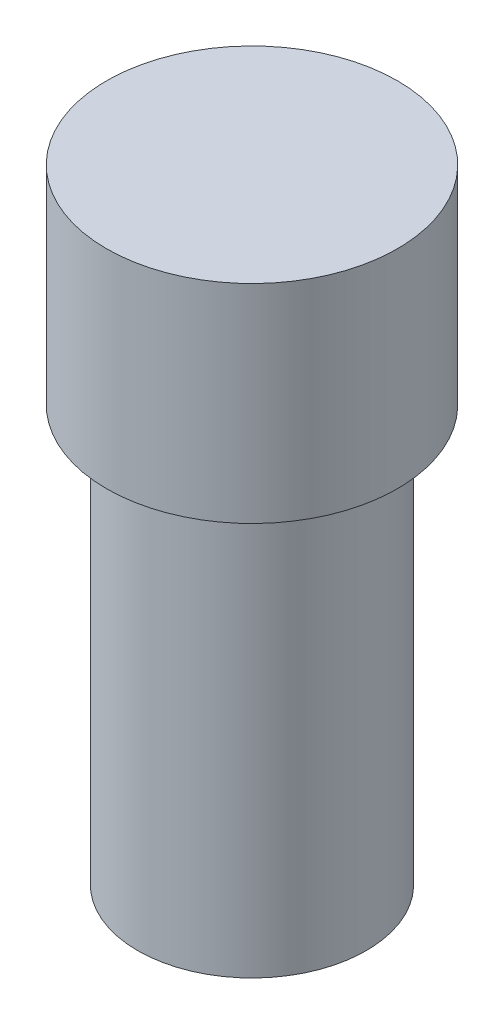
SolidWorks part; units mm, degrees
ref_plane "Front Plane" through (0, 0, 0) normal (0, 0, 1) x (1, 0, 0)
ref_plane "Top Plane" through (0, 0, 0) normal (0, 1, 0) x (1, 0, 0)
ref_plane "Right Plane" through (0, 0, 0) normal (1, 0, 0) x (0, 0, -1)
sketch "Sketch1" plane through (0, 0, 0) normal (0, 1, 0) x (1, 0, 0)
  circle A0 centre (0, 0) radius 2.75
  dimension "D1" = 5.5
extrude "Boss-Extrude1" add sketch "Sketch1" along normal blind 10
sketch "Sketch2" plane through (0, 10, 0) normal (0, 1, 0) x (1, 0, 0)
  circle A0 centre (0, 0) radius 3.5
  dimension "D1" = 7
extrude "Boss-Extrude2" add sketch "Sketch2" along normal blind 5
